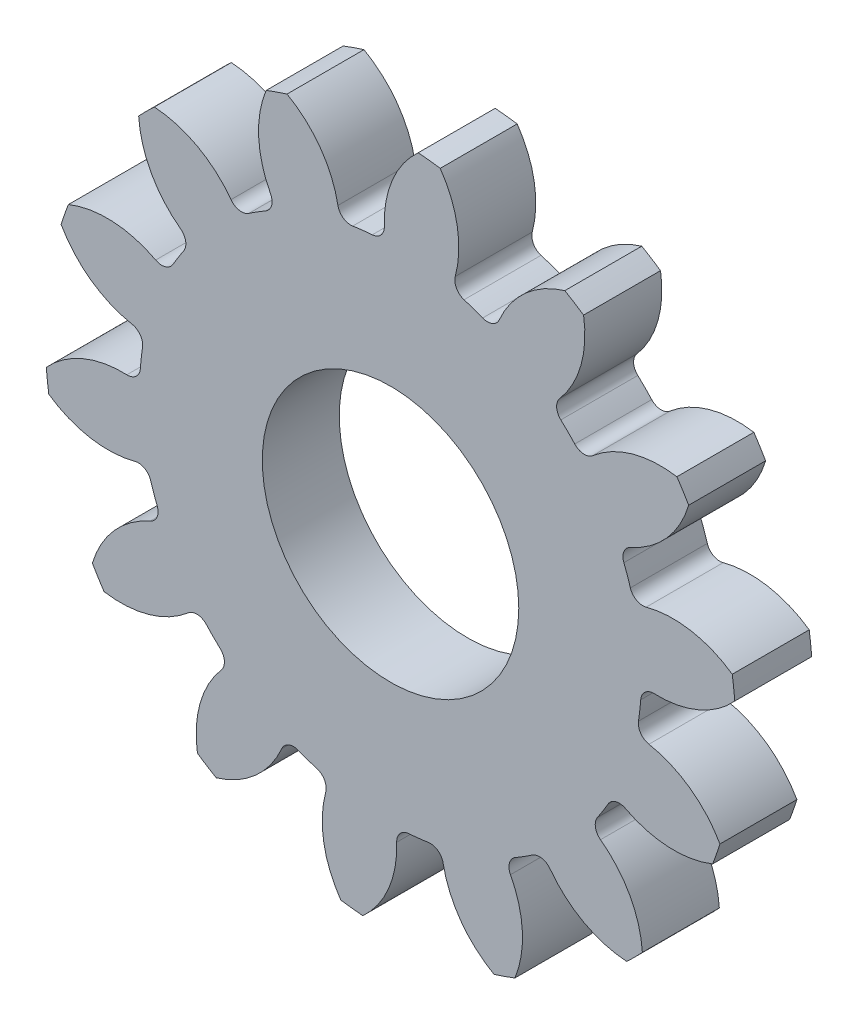
SolidWorks part; units mm, degrees
ref_plane "Alzado" through (0, 0, 0) normal (0, 0, 1) x (1, 0, 0)
ref_plane "Planta" through (0, 0, 0) normal (0, 1, 0) x (1, 0, 0)
ref_plane "Vista lateral" through (0, 0, 0) normal (1, 0, 0) x (0, 0, -1)
sketch "Croquis1" plane through (0, 0, 0) normal (0, 0, 1) x (1, 0, 0)
  circle A0 centre (0, 0) radius 13.462
  dimension "D1" = 26.924
extrude "Saliente-Extruir1" add sketch "Croquis1" along normal blind 3
sketch "Croquis2" plane through (0, 0, 3) normal (0, 0, 1) x (1, 0, 0)
  line L0 (0, 0) -> (0, 11.811) construction
  line L1 (0, 0) -> (4.827, 13.262) construction
  line L2 (0, 0) -> (-1.3208, 11.7369) construction
  line L3 (0, 11.811) -> (3.796, 10.4294) construction
  arc A0 (1.0789, 13.4187) -> (-4.0343, 12.8433) centre (0, 0) ccw
  arc A2 (-0.1906, 9.7771) -> (-1.9872, 9.575) centre (0, 0) ccw
  arc A3 (1.0789, 13.4187) -> (-0.1906, 9.7771) centre (3.796, 10.4294) ccw
  arc A4 (-4.0343, 12.8433) -> (-1.9872, 9.575) centre (-6.019, 9.3249) cw
  dimension "D2" = 19.558
  dimension "D3" = 20
  dimension "D4" = 1.3208
extrude "Cortar-Extruir1" cut sketch "Croquis2" against normal through all
fillet "Redondeo1" radius 0.508 2 edges at (-0.1906, 9.7771, 1.5) (-1.9872, 9.575, 1.5)
pattern_circular "MatrizC1" count 14 over 360 about axis through (0, 0, 0) along (0, 0, 1) of "Redondeo1", "Cortar-Extruir1"
sketch "Croquis3" plane through (0, 0, 3) normal (0, 0, 1) x (1, 0, 0)
  circle A0 centre (0, 0) radius 5
  dimension "D1" = 10
extrude "Cortar-Extruir2" cut sketch "Croquis3" against normal through all
